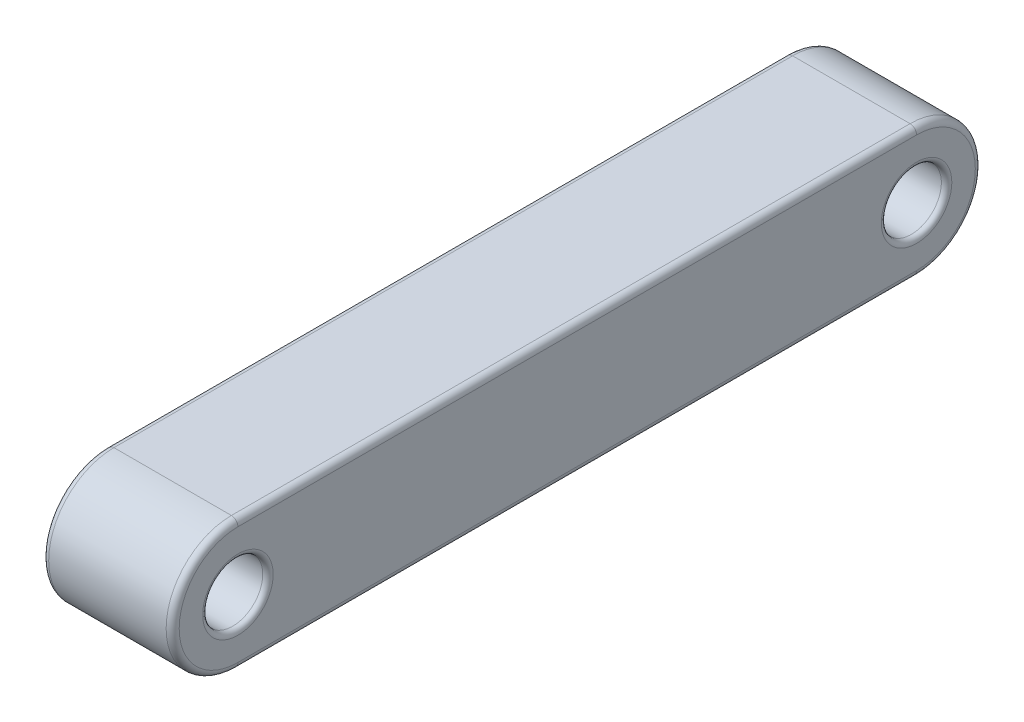
SolidWorks part; units mm, degrees
ref_plane "Front Plane" through (0, 0, 0) normal (0, 0, 1) x (1, 0, 0)
ref_plane "Top Plane" through (0, 0, 0) normal (0, 1, 0) x (1, 0, 0)
ref_plane "Right Plane" through (0, 0, 0) normal (1, 0, 0) x (0, 0, -1)
sketch "Sketch1" plane through (0, 0, 0) normal (1, 0, 0) x (0, 0, -1)
  line L1 (0, 0) -> (11, 0)
  line L2 (0, 0) -> (0, -2.5) construction
  line L3 (0, -2.5) -> (11, -2.5)
  line L4 (11, 0) -> (11, -2.5) construction
  line L5 (0, 0) -> (-1, 0)
  line L6 (0, 0) -> (0, -2.5) construction
  line L7 (0, -2.5) -> (-1, -2.5)
  line L8 (-1, 0) -> (-1, -2.5) construction
  line L9 (11, 0) -> (12, 0)
  line L10 (11, 0) -> (11, -2.5) construction
  line L11 (11, -2.5) -> (12, -2.5)
  line L12 (12, 0) -> (12, -2.5) construction
  line L16 (0, -1.25) -> (-1, -1.25) construction
  line L17 (11, -1.25) -> (12, -1.25) construction
  circle A0 centre (-1, -1.25) radius 0.575
  arc A1 (-1, -2.5) -> (-1, 0) centre (-1, -1.25) cw
  circle A2 centre (12, -1.25) radius 0.575
  arc A3 (12, 0) -> (12, -2.5) centre (12, -1.25) cw
  dimension "D1" = 1.15
  dimension "D4" = 1.15
  dimension "D2" = 2.5
  dimension "D3" = 2.5
  dimension "D5" = 13
  dimension "D6" = 2.5
  dimension "D7" = 1
  dimension "D8" = 1
extrude "Boss-Extrude1" add sketch "Sketch1" along normal blind 2.5 contours A3 L9 L1 L5 A1 L7 L3 L11 A2 A0
fillet "Fillet1" radius 0.125 8 edges at (2.5, -1.25, -13.25) (2.5, 0, -5.5) (2.5, -1.25, 2.25) (0, -1.25, -13.25) (0, 0, -5.5) (0, -1.25, 2.25) (2.5, -2.5, -5.5) (0, -2.5, -5.5)
fillet "Fillet2" radius 0.1 4 edges at (0, -1.25, -12.575) (2.5, -1.25, -12.575) (0, -1.25, 0.425) (2.5, -1.25, 0.425)
